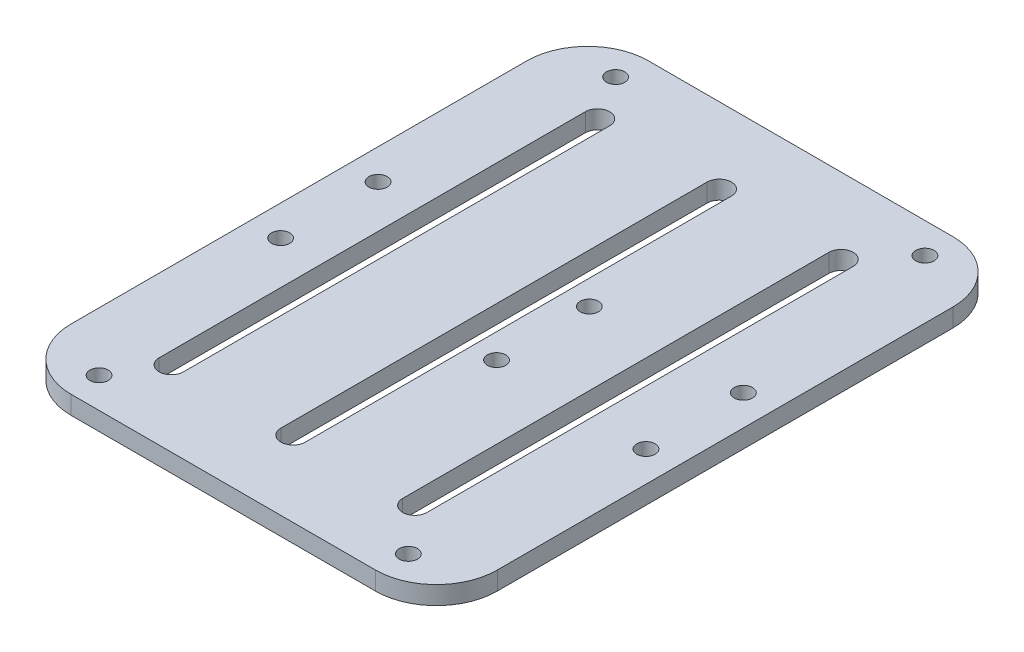
SolidWorks part; units mm, degrees
ref_plane "前视基准面" through (0, 0, 0) normal (0, 0, 1) x (1, 0, 0)
ref_plane "上视基准面" through (0, 0, 0) normal (0, 1, 0) x (1, 0, 0)
ref_plane "右视基准面" through (0, 0, 0) normal (1, 0, 0) x (0, 0, -1)
sketch "草图1" plane through (0, 0, 0) normal (0, 1, 0) x (1, 0, 0)
  line L0 (-20.9571, -35) -> (-20.9571, 35) construction
  line L1 (-30, 8) -> (30, 8) construction
  line L2 (-30, 8) -> (-30, -8) construction
  line L3 (-30, -8) -> (30, -8) construction
  line L4 (30, 8) -> (30, -8) construction
  line L5 (-30, 8) -> (30, -8) construction
  line L6 (-30, -8) -> (30, 8) construction
  line L7 (-25.4, 42.42) -> (25.4, 42.42) construction
  line L8 (-25.4, 42.42) -> (-25.4, -42.42) construction
  line L9 (-25.4, -42.42) -> (25.4, -42.42) construction
  line L10 (25.4, 42.42) -> (25.4, -42.42) construction
  line L11 (-25.4, 42.42) -> (25.4, -42.42) construction
  line L12 (-25.4, -42.42) -> (25.4, 42.42) construction
  line L13 (-25, 47.42) -> (25, 47.42)
  line L14 (-35, 37.42) -> (-35, -37.42)
  line L15 (-25, -47.42) -> (25, -47.42)
  line L16 (35, 37.42) -> (35, -37.42)
  line L17 (-35, 47.42) -> (35, -47.42) construction
  line L18 (-35, -47.42) -> (35, 47.42) construction
  line L19 (-22.9571, -35) -> (-22.9571, 35)
  line L20 (-18.9571, -35) -> (-18.9571, 35)
  line L21 (-0.9571, -35) -> (-0.9571, 35) construction
  line L22 (-2.9571, -35) -> (-2.9571, 35)
  line L23 (1.0429, -35) -> (1.0429, 35)
  line L24 (19.0429, -35) -> (19.0429, 35) construction
  line L25 (17.0429, -35) -> (17.0429, 35)
  line L26 (21.0429, -35) -> (21.0429, 35)
  line L27 (-55, 0) -> (55, 0) construction
  line L28 (-6.35, 10.845) -> (6.35, 10.845) construction
  line L29 (-6.35, 10.845) -> (-6.35, -10.845) construction
  line L30 (-6.35, -10.845) -> (6.35, -10.845) construction
  line L31 (6.35, 10.845) -> (6.35, -10.845) construction
  line L32 (-6.35, 10.845) -> (6.35, -10.845) construction
  line L33 (-6.35, -10.845) -> (6.35, 10.845) construction
  circle A0 centre (-30, 8) radius 1.5
  circle A1 centre (30, 8) radius 1.5
  circle A2 centre (-30, -8) radius 1.5
  circle A3 centre (30, -8) radius 1.5
  circle A4 centre (-25.4, 42.42) radius 1.5
  circle A5 centre (25.4, 42.42) radius 1.5
  circle A6 centre (-25.4, -42.42) radius 1.5
  circle A7 centre (25.4, -42.42) radius 1.5
  arc A8 (-35, -37.42) -> (-25, -47.42) centre (-25, -37.42) ccw
  arc A9 (25, -47.42) -> (35, -37.42) centre (25, -37.42) ccw
  arc A10 (35, 37.42) -> (25, 47.42) centre (25, 37.42) ccw
  arc A11 (-35, 37.42) -> (-25, 47.42) centre (-25, 37.42) cw
  arc A12 (-22.9571, -35) -> (-18.9571, -35) centre (-20.9571, -35) ccw
  arc A13 (-18.9571, 35) -> (-22.9571, 35) centre (-20.9571, 35) ccw
  arc A14 (-2.9571, -35) -> (1.0429, -35) centre (-0.9571, -35) ccw
  arc A15 (1.0429, 35) -> (-2.9571, 35) centre (-0.9571, 35) ccw
  arc A16 (17.0429, -35) -> (21.0429, -35) centre (19.0429, -35) ccw
  arc A17 (21.0429, 35) -> (17.0429, 35) centre (19.0429, 35) ccw
  circle A18 centre (5.08, -7.62) radius 1.5
  circle A19 centre (5.08, 7.62) radius 1.5
  point P0 (0, 0)
  point P10 (0, 0)
  point P19 (0, 0)
  point P38 (-20.9571, 0)
  point P43 (0, 0)
  point P47 (-0.9571, 0)
  point P54 (19.0429, 0)
  dimension "D3" = 3
  dimension "D4" = 3
  dimension "D5" = 3
  dimension "D6" = 3
  dimension "D9" = 3
  dimension "D10" = 3
  dimension "D11" = 3
  dimension "D12" = 3
  dimension "D15" = 10
  dimension "D16" = 2
  dimension "D20" = 3
  dimension "D21" = 2.54
  dimension "D22" = 7.62
  dimension "D1" = 60
  dimension "D2" = 16
  dimension "D7" = 50.8
  dimension "D8" = 84.84
  dimension "D13" = 5
  dimension "D14" = 5
  dimension "D17" = 70
  dimension "D18" = 12.7
  dimension "D19" = 21.69
extrude "凸台-拉伸1" add sketch "草图1" along normal blind 3
